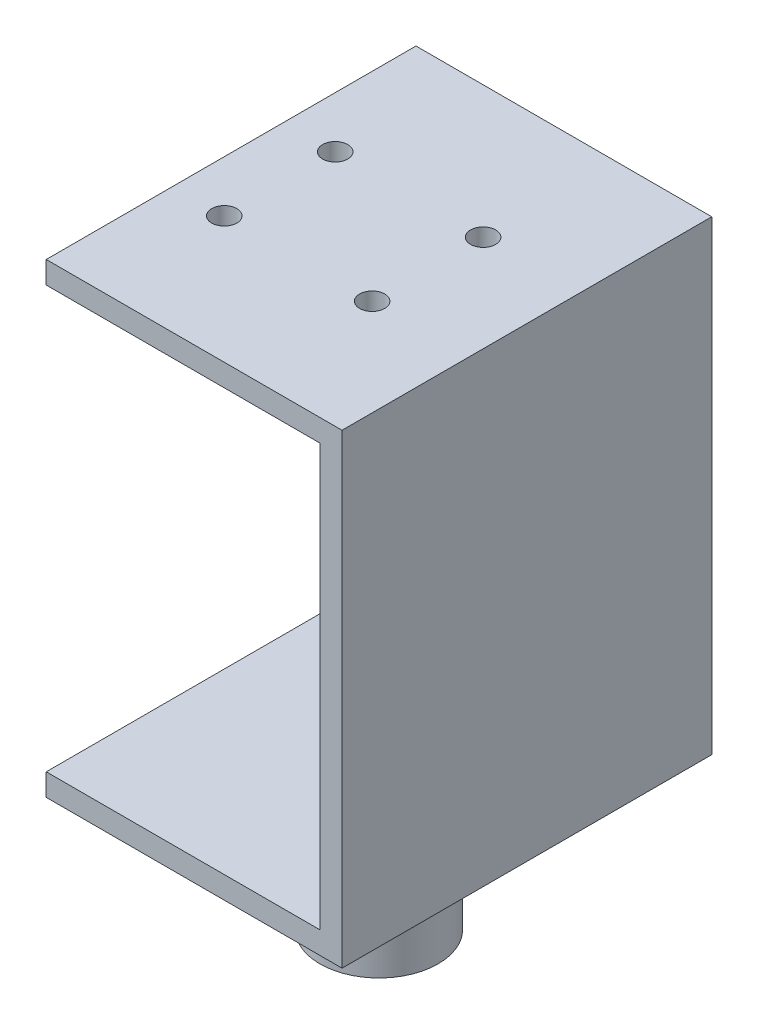
SolidWorks part; units mm, degrees
ref_plane "Front Plane" through (0, 0, 0) normal (0, 0, 1) x (1, 0, 0)
ref_plane "Top Plane" through (0, 0, 0) normal (0, 1, 0) x (1, 0, 0)
ref_plane "Right Plane" through (0, 0, 0) normal (1, 0, 0) x (0, 0, -1)
sketch "Sketch2" plane through (0, 0, 0) normal (0, 0, 1) x (1, 0, 0)
  line L1 (-20, 20) -> (20, 20)
  line L4 (20, 20) -> (20, -40)
  line L5 (-20, 20) -> (-17, 16.025) construction
  line L7 (-20, 17) -> (17, 17)
  line L8 (-17, 17) -> (-17, 16.025)
  line L10 (17, 17) -> (17, -40)
  line L11 (17, -40) -> (-20, -40)
  line L12 (20, -40) -> (20, -43)
  line L13 (20, -43) -> (-20, -43)
  line L14 (17, 16.025) -> (20, 20) construction
  line L16 (-20, 20) -> (-20, 17)
  line L17 (-20, -40) -> (-20, -43)
  dimension "D1" = 3
  dimension "D2" = 3
  dimension "D3" = 40
  dimension "D4" = 60
  dimension "D5" = 3
  dimension "D6" = 40
extrude "Boss-Extrude1" add sketch "Sketch2" along normal mid plane 50 contours L1 L4 L12 L13 L17 L11 L10 L7 L16
sketch "Sketch3" plane through (0, -43, 0) normal (0, -1, 0) x (1, 0, 0)
  circle A0 centre (0, 0) radius 8
  dimension "D1" = 16
extrude "Boss-Extrude2" add sketch "Sketch3" along normal blind 18
hole_wizard "M3 Clearance Hole1" positions "Sketch4" profile "Sketch5" hole size "M3" standard "ISO"
sketch "Sketch4" plane through (0, 20, 0) normal (0, 1, 0) x (1, 0, 0)
  point P0 (-13.0726, -7.85)
  point P3 (-13.0726, 7.15)
  point P6 (6.9274, -7.85)
  point P9 (6.9274, 7.15)
sketch "Sketch5" plane through (-13.0726, 20, 7.85) normal (1, 0, 0) x (0, 0, 1)
  line L0 (0, 0) -> (0, 4.0205)
  line L1 (0, 4.0205) -> (1.7, 2.999)
  line L2 (1.7, 2.999) -> (1.7, 0)
  line L5 (1.7, 0) -> (0, 0)
  line L10 (0, 4.0205) -> (-1.7, 2.999) construction
  line L11 (0, -6.35) -> (0, 107.95) construction
  dimension "Hole Dia." = 3.4
  dimension "Hole Depth" = 2.999
  dimension "Drill Angle" = 118
